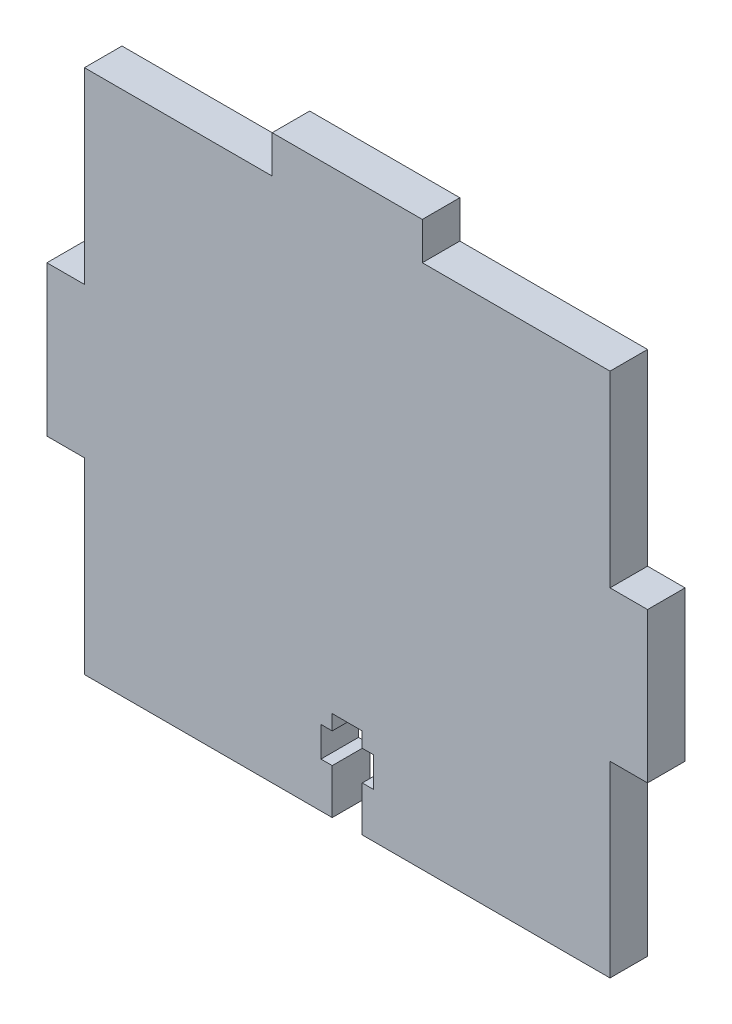
SolidWorks part; units mm, degrees
ref_plane "Front Plane" through (0, 0, 0) normal (0, 0, 1) x (1, 0, 0)
ref_plane "Top Plane" through (0, 0, 0) normal (0, 1, 0) x (1, 0, 0)
ref_plane "Right Plane" through (0, 0, 0) normal (1, 0, 0) x (0, 0, -1)
sketch "Sketch1" plane through (0, 0, 0) normal (0, 0, 1) x (1, 0, 0)
  line L0 (-27.1223, 0) -> (33.5025, 0) construction
  line L1 (-35, 35) -> (-10, 35)
  line L2 (-35, 35) -> (-35, 10)
  line L3 (-35, -35) -> (35, -35)
  line L4 (35, 35) -> (35, 10)
  line L5 (-35, 35) -> (35, -35) construction
  line L6 (-35, -35) -> (35, 35) construction
  line L7 (0, 34.9212) -> (0, -44.6612) construction
  line L8 (-10, 35) -> (-10, 40)
  line L9 (35, 10) -> (40, 10)
  line L10 (40, 10) -> (40, -10)
  line L11 (35, -10) -> (40, -10)
  line L12 (-27.1223, 10) -> (33.5025, 10) construction
  line L13 (-10, 40) -> (10, 40)
  line L14 (10, 35) -> (10, 40)
  line L15 (-35, -10) -> (-40, -10)
  line L16 (-40, -10) -> (-40, 10)
  line L17 (-35, 10) -> (-40, 10)
  line L18 (10, 35) -> (35, 35)
  line L19 (-35, -10) -> (-35, -35)
  line L20 (35, -10) -> (35, -35)
  point P0 (0, 0)
  point P10 (-27.1223, -10)
  point P11 (33.5025, -10)
  point P28 (0, 0)
  dimension "D1" = 70
  dimension "D2" = 3
  dimension "D4" = 5
  dimension "D5" = 5
  dimension "D3" = 10
extrude "Boss-Extrude1" add sketch "Sketch1" along normal blind 5
sketch "Sketch2" plane through (0, 0, 5) normal (0, 0, 1) x (1, 0, 0)
  line L0 (0, 31.6803) -> (0, -30.8838) construction
  line L1 (-2, -35) -> (-2, -29)
  line L2 (-35, -35) -> (35, -35) construction
  line L3 (-2, -29) -> (-3.5, -29)
  line L4 (-3.5, -29) -> (-3.5, -25)
  line L5 (-3.5, -25) -> (-2, -25)
  line L6 (-2, -25) -> (-2, -23)
  line L7 (-2, -23) -> (2, -23)
  line L8 (2, -23) -> (2, -25)
  line L9 (2, -25) -> (3.5, -25)
  line L10 (3.5, -25) -> (3.5, -29)
  line L11 (3.5, -29) -> (2, -29)
  line L12 (2, -29) -> (2, -35)
  line L13 (2, -35) -> (-2, -35)
  point P9 (0, -35)
  point P18 (0, -23)
  dimension "D1" = 12
  dimension "D2" = 6
  dimension "D3" = 4
  dimension "D4" = 1.5
  dimension "D5" = 4
other "AlignGroup1"
extrude "Cut-Extrude1" cut sketch "Sketch2" against normal blind 10
